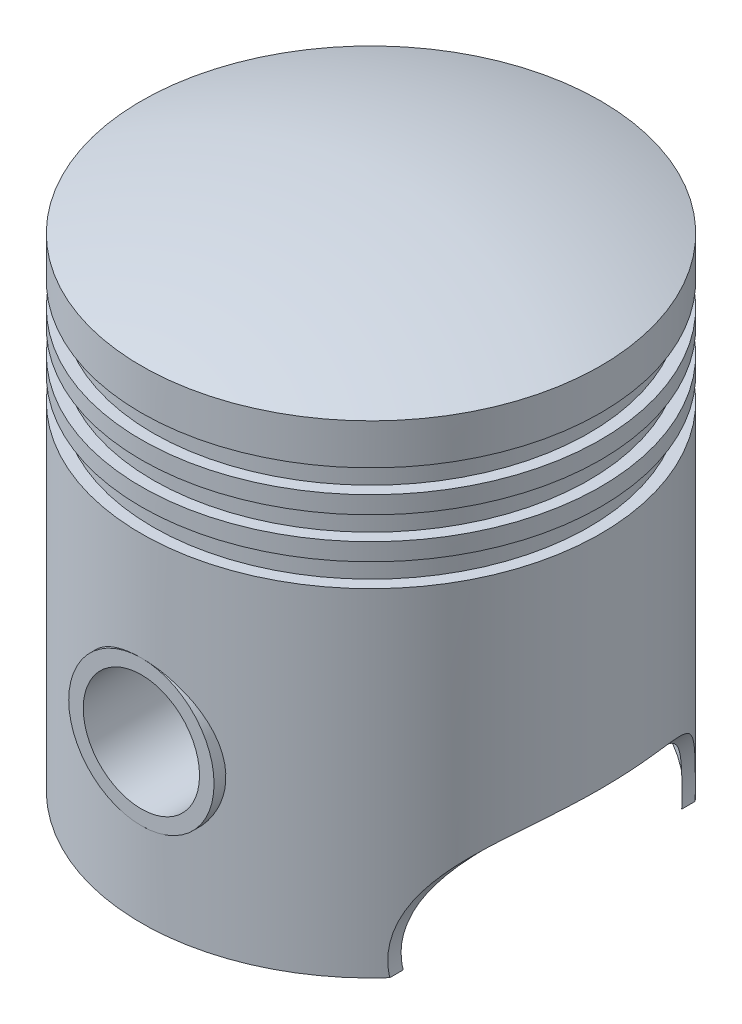
SolidWorks part; units mm, degrees
material "Magnesium Alloy"
ref_plane "Front Plane" through (0, 0, 0) normal (0, 0, 1) x (1, 0, 0)
ref_plane "Top Plane" through (0, 0, 0) normal (0, 1, 0) x (1, 0, 0)
ref_plane "Right Plane" through (0, 0, 0) normal (1, 0, 0) x (0, 0, -1)
sketch "Sketch1" plane through (0, 0, 0) normal (1, 0, 0) x (0, 0, -1)
  line L0 (0, 0) -> (0, 90)
  line L1 (0, 0) -> (39.5, 0)
  line L2 (39.5, 0) -> (39.5, 83)
  arc A0 (0, 90) -> (39.5, 83) centre (0, -24.9464) cw
  dimension "D1" = 39.5
  dimension "D2" = 90
  dimension "D3" = 7
revolve "Revolve1" add sketch "Sketch1" angle 360 about L0
sketch "Sketch2" plane through (0, 0, 0) normal (1, 0, 0) x (0, 0, -1)
  line L0 (0, 0) -> (0, 85)
  line L1 (0, 0) -> (38, 0)
  line L2 (-39.5, 0) -> (39.5, 0) construction
  line L3 (38, 0) -> (38, 47)
  arc A0 (0, 85) -> (38, 47) centre (0, 47) cw
  dimension "D2" = 85
  dimension "D3" = 38
revolve "Cut-Revolve1" cut sketch "Sketch2" angle 360 about L0
sketch "Sketch3" plane through (0, 0, 0) normal (0, 0, 1) x (1, 0, 0)
  line L0 (0, -1000) -> (0, 49000) construction
  circle A0 centre (0, 27) radius 12.5
  dimension "D1" = 25
  dimension "D2" = 27
extrude "Boss-Extrude1" add sketch "Sketch3" along normal through all from offset 10
sketch "Sketch4" plane through (0, 0, 39.5) normal (0, 0, 1) x (1, 0, 0)
  circle A0 centre (0, 27) radius 10
  dimension "D1" = 20
extrude "Cut-Extrude1" cut sketch "Sketch4" against normal up to next (29.5 mm away)
mirror "Mirror1" about plane through (0, 0, 0) normal (1, 0, 0) of "Cut-Extrude1", "Boss-Extrude1"
mirror "Mirror2" about plane through (0, 0, 0) normal (0, 0, 1) of "Cut-Extrude1", "Boss-Extrude1"
sketch "Sketch5" plane through (0, 0, 0) normal (0, 0, 1) x (1, 0, 0)
  line L0 (-39.5, 83) -> (-39.5, 0) construction
  line L1 (-41.5, 76) -> (-37.5, 76)
  line L2 (-41.5, 76) -> (-41.5, 72)
  line L3 (-41.5, 72) -> (-37.5, 72)
  line L4 (-37.5, 76) -> (-37.5, 72)
  line L5 (-41.5, 76) -> (-37.5, 72) construction
  line L6 (-41.5, 72) -> (-37.5, 76) construction
  line L7 (39.5, 83) -> (-39.5, 83) construction
  line L8 (-41.5, 69) -> (-37.5, 69)
  line L9 (-41.5, 69) -> (-41.5, 65)
  line L10 (-41.5, 65) -> (-37.5, 65)
  line L11 (-37.5, 69) -> (-37.5, 65)
  line L12 (-41.5, 69) -> (-37.5, 65) construction
  line L13 (-41.5, 65) -> (-37.5, 69) construction
  line L14 (-41.5, 62) -> (-37.5, 62)
  line L15 (-41.5, 62) -> (-41.5, 58)
  line L16 (-41.5, 58) -> (-37.5, 58)
  line L17 (-37.5, 62) -> (-37.5, 58)
  line L18 (-41.5, 62) -> (-37.5, 58) construction
  line L19 (-41.5, 58) -> (-37.5, 62) construction
  point P0 (-39.5, 74)
  point P7 (-39.5, 67)
  point P12 (-39.5, 60)
  dimension "D1" = 4
  dimension "D2" = 4
  dimension "D3" = 4
  dimension "D4" = 4
  dimension "D5" = 4
  dimension "D6" = 4
  dimension "D7" = 11
  dimension "D8" = 11
  dimension "D9" = 11
revolve "Cut-Revolve5" cut sketch "Sketch5" angle 360 about axis through (0, 0, 0) along (0, -1, 0)
sketch "Sketch6" plane through (0, 0, 0) normal (0, 0, 1) x (1, 0, 0)
  line L1 (39.5, 0) -> (29.5, 0)
  line L2 (39.5, 0) -> (39.5, 20)
  arc A1 (29.5, 0) -> (39.5, 20) centre (49.3324, 2.5838) cw
  dimension "D3" = 20
  dimension "D1" = 20
  dimension "D2" = 10
extrude "Cut-Extrude2" cut sketch "Sketch6" against normal through all both and the other way through all
mirror "Mirror3" about plane through (0, 0, 0) normal (1, 0, 0) of "Cut-Extrude2"
